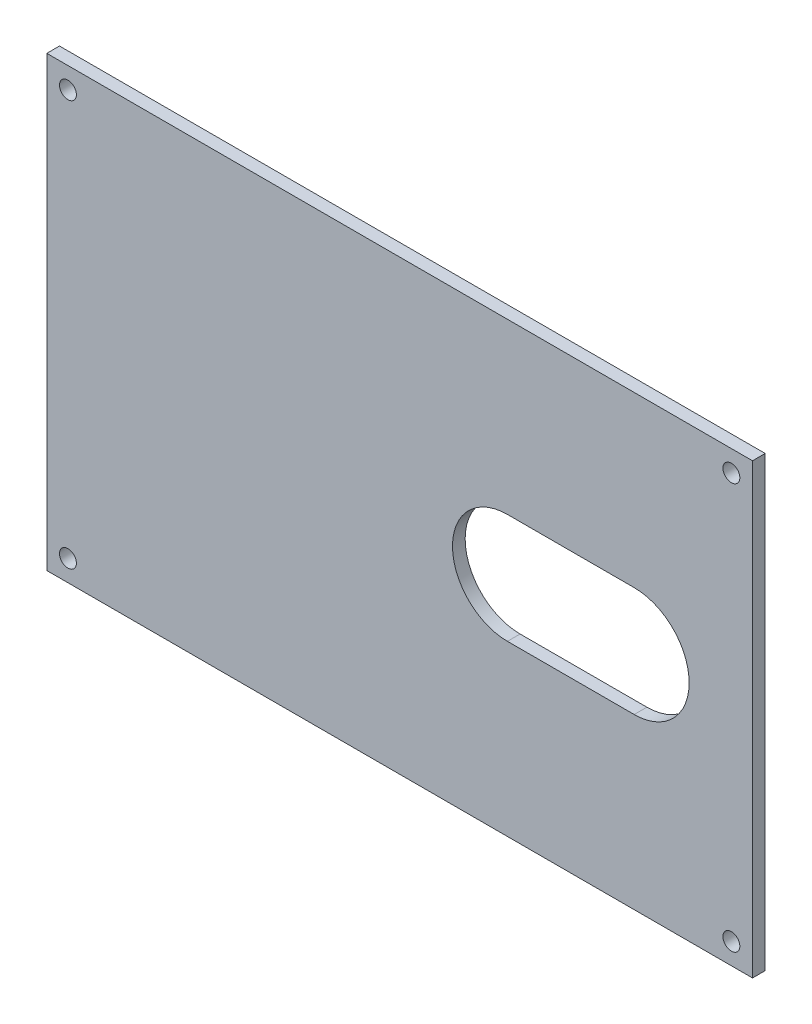
SolidWorks part; units mm, degrees
material "Acrylic (Medium-high impact)"
ref_plane "Front Plane" through (0, 0, 0) normal (0, 0, 1) x (1, 0, 0)
ref_plane "Top Plane" through (0, 0, 0) normal (0, 1, 0) x (1, 0, 0)
ref_plane "Right Plane" through (0, 0, 0) normal (1, 0, 0) x (0, 0, -1)
sketch "Sketch1" plane through (0, 0, 0) normal (0, 0, 1) x (-1, 0, 0)
  line L19 (-136, 63) -> (-106, 63)
  line L21 (-106, 37) -> (-136, 37)
  line L27 (-164, -3) -> (3, -3)
  line L28 (3, -3) -> (3, 103)
  line L29 (3, 103) -> (-164, 103)
  line L30 (-164, 103) -> (-164, -3)
  circle A0 centre (-159, 98) radius 2
  circle A1 centre (-2, 98) radius 2
  circle A2 centre (-2, 2) radius 2
  circle A3 centre (-159, 2) radius 2
  arc A4 (-136, 63) -> (-136, 37) centre (-136, 50) ccw
  arc A5 (-106, 37) -> (-106, 63) centre (-106, 50) ccw
  dimension "D2" = 30
extrude "Boss-Extrude1" add sketch "Sketch1" along normal blind 3
